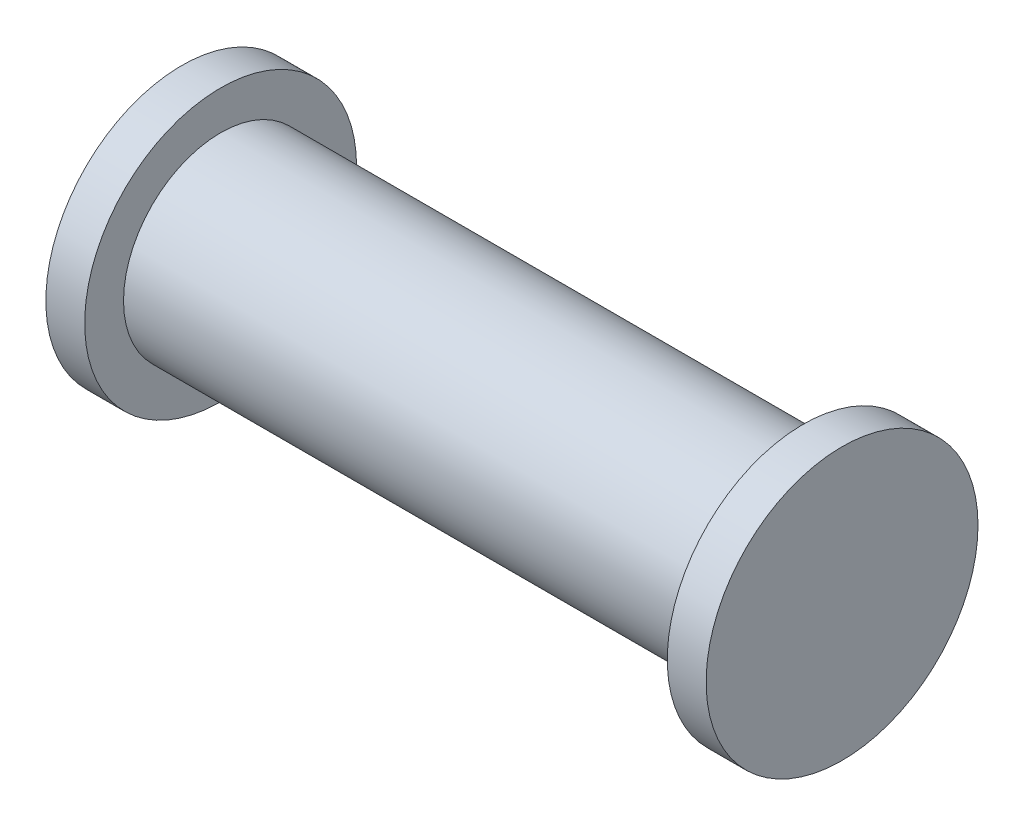
SolidWorks part; units mm, degrees
ref_plane "Front Plane" through (0, 0, 0) normal (0, 0, 1) x (1, 0, 0)
ref_plane "Top Plane" through (0, 0, 0) normal (0, 1, 0) x (1, 0, 0)
ref_plane "Right Plane" through (0, 0, 0) normal (1, 0, 0) x (0, 0, -1)
sketch "Sketch1" plane through (0, 0, 0) normal (1, 0, 0) x (0, 0, -1)
  circle A0 centre (0, 0) radius 12.5
  dimension "D2" = 0
extrude "Boss-Extrude1" add sketch "Sketch1" along normal mid plane 0 separate body
sketch "Sketch4" plane through (37.5, 0, 0) normal (1, 0, 0) x (0, 0, -1)
  circle A0 centre (0, 0) radius 17.5
  dimension "D1" = 0
extrude "Boss-Extrude3" add sketch "Sketch4" along normal blind 5 separate body
mirror "Mirror1" about plane through (0, 0, 0) normal (1, 0, 0) of "Boss-Extrude3"
